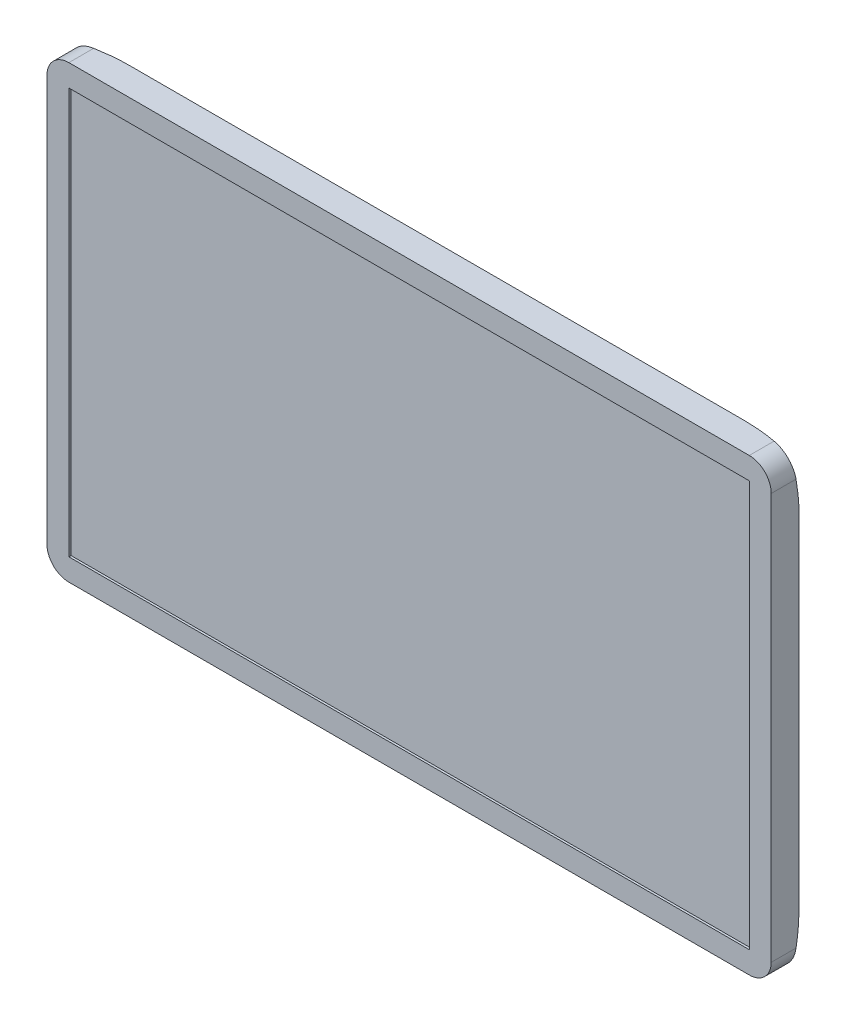
SolidWorks part; units mm, degrees
ref_plane "Plan de face" through (0, 0, 0) normal (0, 0, 1) x (1, 0, 0)
ref_plane "Plan de dessus" through (0, 0, 0) normal (0, 1, 0) x (1, 0, 0)
ref_plane "Plan de droite" through (0, 0, 0) normal (1, 0, 0) x (0, 0, -1)
sketch "Esquisse1" plane through (0, 0, 0) normal (0, 0, 1) x (1, 0, 0)
  line L1 (0, 0) -> (330, 0)
  line L2 (0, 0) -> (0, 205)
  line L3 (0, 205) -> (330, 205)
  line L4 (330, 0) -> (330, 205)
  point P7 (0, 0)
  point P12 (330, 205)
  point P15 (0, 205)
  dimension "D1" = 205
  dimension "D2" = 330
extrude "Boss.-Extru.1" add sketch "Esquisse1" along normal blind 30
chamfer "Chanfrein1" distance 30 angle 30 4 edges at (165, 205, 0) (330, 102.5, 0) (0, 102.5, 0) (165, 0, 0)
fillet "Congé1" radius 50 4 edges at (15, 15, 8.6603) (315, 15, 8.6603) (315, 190, 8.6603) (15, 190, 8.6603)
fillet "Congé3" radius 10 4 edges at (0, 205, 25.5247) (330, 205, 25.5247) (330, 0, 25.5247) (0, 0, 25.5247)
sketch "Esquisse2" plane through (0, 0, 30) normal (0, 0, 1) x (1, 0, 0)
  line L8 (320, 195) -> (10, 195)
  line L9 (10, 195) -> (10, 10)
  line L10 (10, 10) -> (320, 10)
  line L11 (320, 10) -> (320, 195)
  line L12 (320, 195) -> (10, 195)
  line L13 (10, 195) -> (10, 10)
  line L14 (10, 10) -> (320, 10)
  line L15 (320, 10) -> (320, 195)
  dimension "D1" = 10
extrude "Enlèv. mat.-Extru.1" cut sketch "Esquisse2" against normal blind 1
hole_wizard "Dégagement M42" positions "Esquisse4" profile "Esquisse5" hole size "M4" standard "ISO"
sketch "Esquisse4" plane through (0, 0, 0) normal (0, 0, -1) x (-1, 0, 0)
  line L1 (-127.5, 140) -> (-202.5, 140)
  line L2 (-127.5, 140) -> (-127.5, 65)
  line L3 (-127.5, 65) -> (-202.5, 65)
  line L4 (-202.5, 140) -> (-202.5, 65)
  line L5 (-127.5, 140) -> (-202.5, 65) construction
  line L6 (-127.5, 65) -> (-202.5, 140) construction
  line L7 (-36.4586, 36.4586) -> (-293.5414, 168.5414) construction
  ellipse E0 centre (-130, 130) end of major axis (-36.4586, 36.4586) minor radius 50 (-55, 30) -> (-30, 55) ccw construction
  ellipse E1 centre (-200, 75) end of major axis (-106.4586, -18.5414) minor radius 50 (-275, 175) -> (-300, 150) ccw construction
  point P2 (-202.5, 65)
  point P25 (-127.5, 140)
  point P26 (-127.5, 65)
  point P27 (-202.5, 140)
  point P48 (-165, 102.5)
  point P60 (-165, 102.5)
  dimension "D1" = 75
  dimension "D2" = 75
sketch "Esquisse5" plane through (202.5, 65, 0) normal (1, 0, 0) x (0, 1, 0)
  line L0 (0, 0) -> (0, 11.2017)
  line L1 (0, 11.2017) -> (2, 10)
  line L2 (2, 10) -> (2, 0)
  line L5 (2, 0) -> (0, 0)
  line L10 (0, 11.2017) -> (-2, 10) construction
  line L11 (0, -6.35) -> (0, 107.95) construction
  dimension "Diamètre du perçage" = 4
  dimension "Profondeur du perçage" = 10
  dimension "Angle de pointe" = 118
hole_wizard "Dégagement M71" positions "Esquisse7" profile "Esquisse8" hole size "M7" standard "ISO"
sketch "Esquisse7" plane through (0, 0, 0) normal (0, 0, -1) x (-1, 0, 0)
  line L1 (-115, 52.5) -> (-215, 52.5)
  line L2 (-115, 52.5) -> (-115, 152.5)
  line L3 (-115, 152.5) -> (-215, 152.5)
  line L4 (-215, 52.5) -> (-215, 152.5)
  line L5 (-115, 52.5) -> (-215, 152.5) construction
  line L6 (-115, 152.5) -> (-215, 52.5) construction
  line L7 (-127.5, 65) -> (-202.5, 140) construction
  line L8 (-115, 152.5) -> (-165, 42.3138) construction
  line L9 (-165, 42.3138) -> (-215, 152.5) construction
  point P2 (-215, 152.5)
  point P86 (-115, 152.5)
  point P105 (-165, 102.5)
  point P106 (-165, 102.5)
  point P108 (-165, 42.3138)
  dimension "D1" = 100
  dimension "D2" = 100
  dimension "D3" = 121
sketch "Esquisse8" plane through (215, 152.5, 0) normal (1, 0, 0) x (0, 1, 0)
  line L0 (0, 0) -> (0, 7.103)
  line L1 (0, 7.103) -> (3.5, 5)
  line L2 (3.5, 5) -> (3.5, 0)
  line L5 (3.5, 0) -> (0, 0)
  line L10 (0, 7.103) -> (-3.5, 5) construction
  line L11 (0, -6.35) -> (0, 107.95) construction
  dimension "Diamètre du perçage" = 7
  dimension "Profondeur du perçage" = 5
  dimension "Angle de pointe" = 118
sketch "Esquisse9" plane through (0, 0, 0) normal (0, 0, -1) x (-1, 0, 0)
  line L0 (-330, 180) -> (-297.9289, 147.9289)
  line L1 (-295, 140.8579) -> (-295, 64.1421)
  line L2 (-297.9289, 57.0711) -> (-330, 25)
  line L3 (-330, 25) -> (-300, 55) construction
  line L5 (-330, 180) -> (-330, 25)
  line L6 (-330, 25) -> (-300, 55)
  line L7 (-300, 55) -> (-300, 150)
  line L12 (-300, 150) -> (-330, 180)
  line L13 (-330, 180) -> (-330, 25)
  line L17 (-300, 150) -> (-330, 180) construction
  arc A2 (-295, 64.1421) -> (-297.9289, 57.0711) centre (-305, 64.1421) cw
  arc A3 (-297.9289, 147.9289) -> (-295, 140.8579) centre (-305, 140.8579) cw
  point P8 (-289.2511, 121.5043)
  dimension "D2" = 35
  dimension "D3" = 10
  dimension "D1" = 0
extrude "Enlèv. mat.-Extru.2" cut sketch "Esquisse9" against normal up to vertex (17.3205 mm away)
